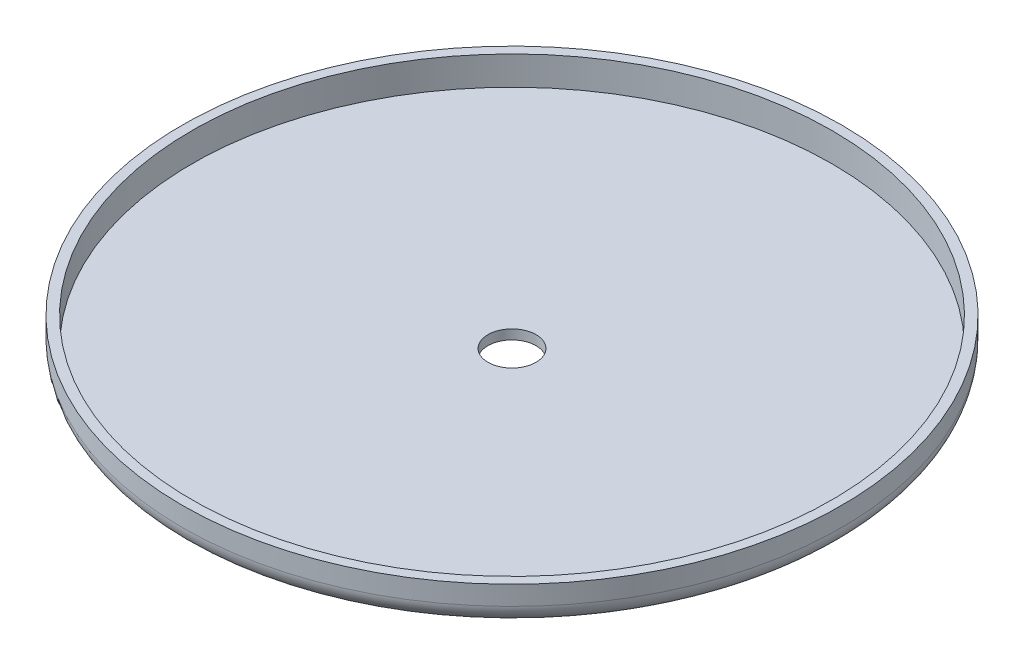
SolidWorks part; units mm, degrees
material "Glass"
ref_plane "Front Plane" through (0, 0, 0) normal (0, 0, 1) x (1, 0, 0)
ref_plane "Top Plane" through (0, 0, 0) normal (0, 1, 0) x (1, 0, 0)
ref_plane "Right Plane" through (0, 0, 0) normal (1, 0, 0) x (0, 0, -1)
sketch "Sketch1" plane through (0, 0, 0) normal (0, 1, 0) x (1, 0, 0)
  circle A0 centre (0, 0) radius 42.291
  circle A1 centre (0, 0) radius 3.175
  dimension "D1" = 84.582
  dimension "D2" = 6.35
extrude "Boss-Extrude1" add sketch "Sketch1" along normal blind 1.27
sketch "Sketch2" plane through (0, 0, 0) normal (0, -1, 0) x (1, 0, 0)
  circle A0 centre (0, 0) radius 43.561
  circle A1 centre (0, 0) radius 42.291
  circle A2 centre (0, 0) radius 42.291 construction
  dimension "D1" = 1.27
extrude "Boss-Extrude2" add sketch "Sketch2" against normal blind 5.08
fillet "Fillet1" radius 2.54 1 edges at (0, 0, -43.561)
